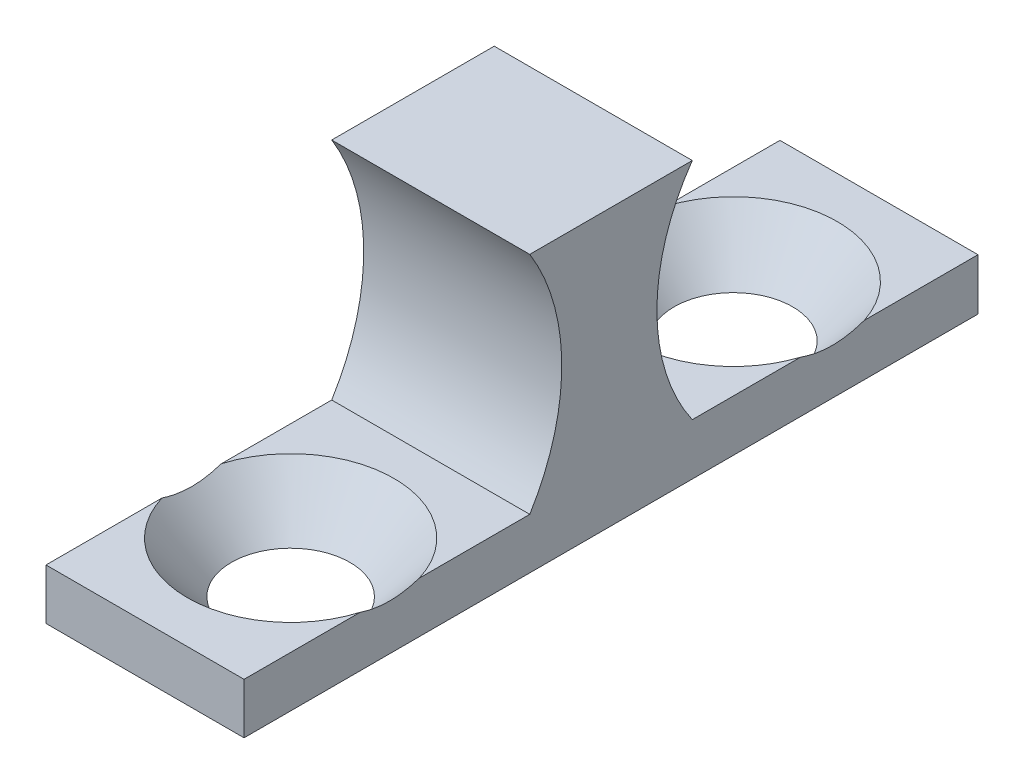
SolidWorks part; units mm, degrees
ref_plane "Front Plane" through (0, 0, 0) normal (0, 0, 1) x (1, 0, 0)
ref_plane "Top Plane" through (0, 0, 0) normal (0, 1, 0) x (1, 0, 0)
ref_plane "Right Plane" through (0, 0, 0) normal (1, 0, 0) x (0, 0, -1)
sketch "Sketch2" plane through (0, 0, 0) normal (1, 0, 0) x (0, 0, -1)
  line L0 (-2.0491, 1.5946) -> (-11.7821, 1.5946)
  line L1 (3.4881, 1.62) -> (13.221, 1.62)
  line L2 (-11.7821, 1.5946) -> (-11.7821, -0.1326)
  line L3 (-11.7821, -0.1326) -> (13.221, -0.1326)
  line L4 (13.221, 1.62) -> (13.221, -0.1326)
  line L5 (-2.0491, 9.2654) -> (3.4881, 9.2654)
  line L6 (-2.0491, 9.2654) -> (-2.0491, 1.5946)
  line L8 (3.4881, 9.2654) -> (3.4881, 1.62)
  dimension "D1" = 1.7272
  dimension "D2" = 1.7526
  dimension "D3" = 7.6708
  dimension "D4" = 9.398
  dimension "length" = 25.0031
  dimension "D5" = 5.5372
  dimension "D6" = 9.733
extrude "Boss-Extrude2" add sketch "Sketch2" along normal blind 6.7469
sketch "Sketch9" plane through (6.7469, 0, 0) normal (1, 0, 0) x (0, 0, -1)
  line L0 (-2.0491, 9.2654) -> (-2.0491, 1.5946)
  line L1 (3.4881, 9.2654) -> (3.4881, 1.62)
  arc A0 (-2.0491, 9.2654) -> (-2.0491, 1.5946) centre (-8.2478, 5.43) cw
  arc A1 (3.4881, 9.2654) -> (3.4881, 1.62) centre (8.9419, 5.4427) ccw
extrude "Cut-Extrude1" cut sketch "Sketch9" against normal up to next
hole_wizard "CSK for #6 Flat Head Machine Screw1" positions "Sketch8" profile "Sketch7" countersink size "#6" standard "Ansi Inch" end condition through all
sketch "Sketch8" plane through (0, 1.62, 0) normal (0, 1, 0) x (-1, 0, 0)
  line L0 (-6.7469, -13.221) -> (0, -13.221) construction
  line L1 (-6.7469, -13.221) -> (-6.7469, -3.4881) construction
  line L2 (-6.7469, 2.0491) -> (-6.7469, 11.7821) construction
  point P0 (-3.3748, -8.2601)
  point P1 (-3.3734, 6.8212)
  point P4 (-3.3734, -13.221)
  point P7 (-6.7469, -8.3545)
  dimension "D1" = 15.0812
  dimension "D2" = 4.9609
  dimension "D3" = 3.3734
  dimension "D4" = 3.3734
sketch "Sketch7" plane through (3.3748, 1.62, -8.2601) normal (1, 0, 0) x (0, 0, 1)
  line L0 (0, 0) -> (0, 1.7526)
  line L1 (0, 1.7526) -> (1.8986, 1.7526)
  line L2 (1.8986, 1.7526) -> (1.8986, 1.892)
  line L3 (1.8986, 1.892) -> (3.5433, 0)
  line L5 (3.5433, 0) -> (0, 0)
  line L6 (-1.8987, 1.892) -> (-3.5433, 0) construction
  line L11 (0, -6.35) -> (0, 107.95) construction
  dimension "Thru Hole Dia." = 3.7973
  dimension "Thru Hole Depth" = 1.7526
  dimension "Near C'Sink Dia." = 7.0866
  dimension "Near C'Sink Angle" = 82
equation "\"D6@Sketch2\" = (\"length@Sketch2\"-\"D5@Sketch2\")/2"
equation "\"D2@Sketch8\" = (\"length@Sketch2\"-\"D1@Sketch8\")/2"
equation "\"D3@Sketch8\" = \"RD1@Annotations\"/2"
equation "\"D4@Sketch8\" = \"D3@Sketch8\""
